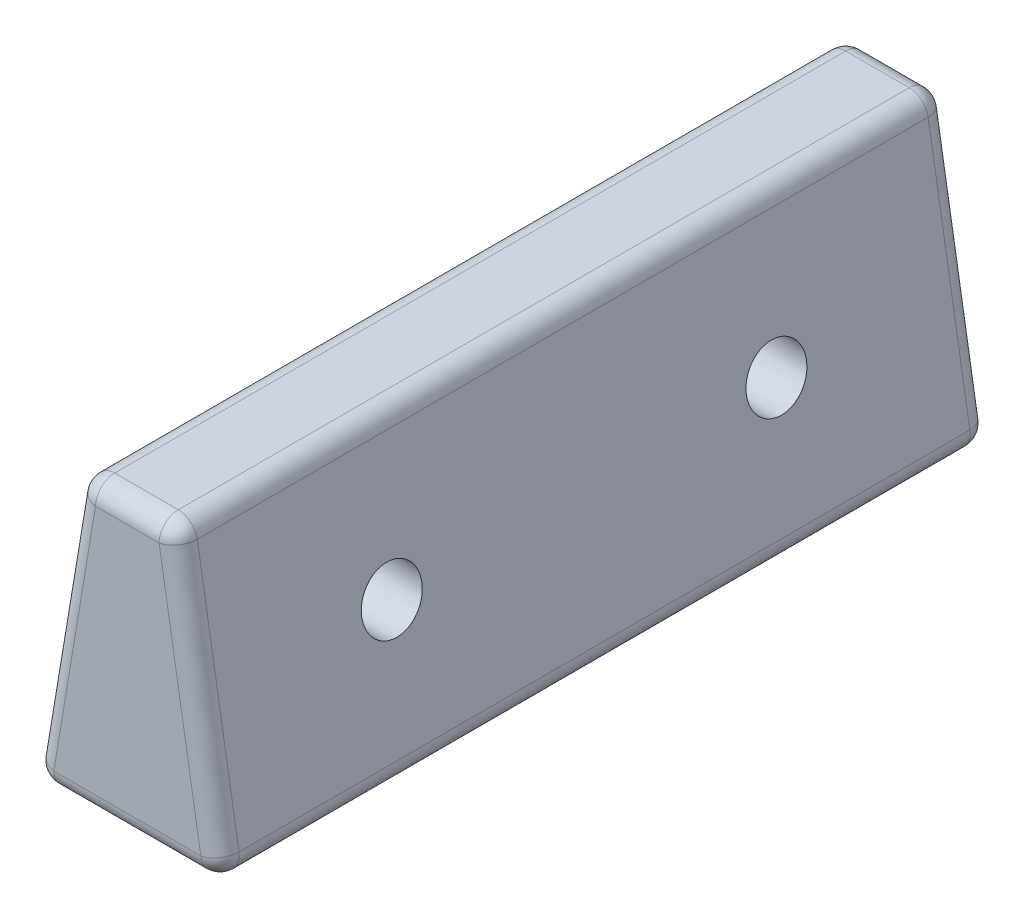
SolidWorks part; units mm, degrees
ref_plane "Front Plane" through (0, 0, 0) normal (0, 0, 1) x (1, 0, 0)
ref_plane "Top Plane" through (0, 0, 0) normal (0, 1, 0) x (1, 0, 0)
ref_plane "Right Plane" through (0, 0, 0) normal (1, 0, 0) x (0, 0, -1)
sketch "Sketch3" plane through (0, 0, 0) normal (0, 0, 1) x (1, 0, 0)
  line L0 (-12.7, 0) -> (12.7, 0)
  line L1 (12.7, 0) -> (6.35, 38.1)
  line L2 (6.35, 38.1) -> (-6.35, 38.1)
  line L3 (-6.35, 38.1) -> (-12.7, 0)
  line L4 (0, 0) -> (0, 38.1) construction
  point P4 (0, 0)
  dimension "D1" = 25.4
  dimension "D2" = 12.7
  dimension "D3" = 90
  dimension "D4" = 38.1
extrude "Boss-Extrude1" add sketch "Sketch3" along normal mid plane 101.6
sketch "Sketch4" plane through (0, 0, 0) normal (1, 0, 0) x (0, 0, -1)
  line L1 (-50.8, 0) -> (-50.8, 38.1) construction
  line L2 (50.8, 0) -> (50.8, 38.1) construction
  line L3 (-50.8, 0) -> (50.8, 0) construction
  circle A0 centre (-25.4, 19.05) radius 3.9687
  circle A1 centre (25.4, 19.05) radius 3.9688
  dimension "D3" = 7.9375
  dimension "D4" = 7.9375
  dimension "D5" = 25.4
  dimension "D1" = 19.05
  dimension "D2" = 19.05
  dimension "D6" = 25.4
fillet "Fillet1" radius 2.54 12 edges at (-9.525, 19.05, -50.8) (0, 0, -50.8) (-12.7, 0, 0) (0, 0, 50.8) (9.525, 19.05, -50.8) (0, 38.1, -50.8) (0, 38.1, 50.8) (-9.525, 19.05, 50.8) (12.7, 0, 0) (9.525, 19.05, 50.8) (-6.35, 38.1, 0) (6.35, 38.1, 0)
extrude "Cut-Extrude1" cut sketch "Sketch4" against normal through all both and the other way through all
